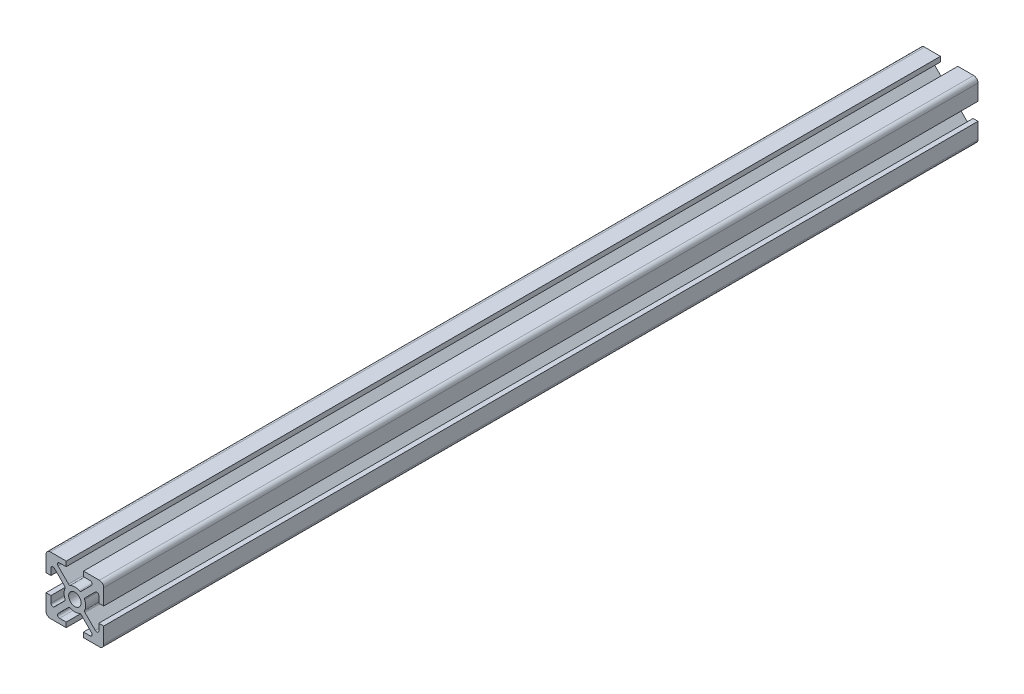
SolidWorks part; units mm, degrees
material "6063-T5"
ref_plane "Face" through (0, 0, 0) normal (0, 0, 1) x (1, 0, 0)
ref_plane "Dessus" through (0, 0, 0) normal (0, 1, 0) x (1, 0, 0)
ref_plane "Droite" through (0, 0, 0) normal (1, 0, 0) x (0, 0, -1)
sketch "Esquisse1" plane through (0, 0, 0) normal (0, 0, 1) x (1, 0, 0)
  line L0 (-3, 10) -> (-8.5, 10)
  line L2 (-3, -10) -> (-3, -8.3)
  line L3 (-3, -8.3) -> (-5.2994, -8.3)
  line L4 (-5.7944, -7.105) -> (-2.1755, -3.4861)
  line L6 (2.1755, -3.4861) -> (5.7944, -7.105)
  line L7 (5.2994, -8.3) -> (3, -8.3)
  line L8 (3, -8.3) -> (3, -10)
  line L11 (3, -10) -> (8.5, -10)
  line L12 (10, -8.5) -> (10, -3)
  line L15 (10, -3) -> (8.3, -3)
  line L16 (8.3, -3) -> (8.3, -5.2994)
  line L17 (7.105, -5.7944) -> (3.4861, -2.1755)
  line L20 (3.4861, 2.1755) -> (7.105, 5.7944)
  line L21 (8.3, 5.2994) -> (8.3, 3)
  line L22 (8.3, 3) -> (10, 3)
  line L25 (10, 3) -> (10, 8.5)
  line L26 (8.5, 10) -> (3.5, 10)
  line L29 (3, 10) -> (3, 8.3)
  line L30 (3, 8.3) -> (5.2994, 8.3)
  line L31 (5.7944, 7.105) -> (2.1755, 3.4861)
  line L34 (-2.1755, 3.4861) -> (-5.7944, 7.105)
  line L35 (-5.2994, 8.3) -> (-3, 8.3)
  line L36 (-3, 8.3) -> (-3, 10)
  line L39 (3.5, 10) -> (3, 10)
  line L40 (-10, 8.5) -> (-10, 3)
  line L43 (-10, 3) -> (-8.3, 3)
  line L44 (-8.3, 3) -> (-8.3, 5.2994)
  line L45 (-7.105, 5.7944) -> (-3.4861, 2.1755)
  line L48 (-3.4861, -2.1755) -> (-7.105, -5.7944)
  line L49 (-8.3, -5.2994) -> (-8.3, -3)
  line L50 (-8.3, -3) -> (-10, -3)
  line L53 (-10, -3) -> (-10, -8.5)
  line L54 (-8.5, -10) -> (-3, -10)
  line L55 (13.1941, 0) -> (-16.3684, 0) construction
  line L56 (0, 3.75) -> (0, -15.1011) construction
  line L58 (5.7944, 5.7944) -> (-5.2994, -5.2994) construction
  line L59 (5.7944, -5.7944) -> (-5.4107, 5.4107) construction
  circle A0 centre (0, 0) radius 2.15
  arc A1 (-5.2994, -8.3) -> (-5.7944, -7.105) centre (-5.2994, -7.6) cw
  arc A2 (-2.1755, -3.4861) -> (-1.6076, -3.388) centre (-1.8219, -3.8397) cw
  arc A3 (-1.6076, -3.388) -> (1.6076, -3.388) centre (0, 0) ccw
  arc A5 (1.6076, -3.388) -> (2.1755, -3.4861) centre (1.8219, -3.8397) cw
  arc A6 (5.7944, -7.105) -> (5.2994, -8.3) centre (5.2994, -7.6) cw
  arc A7 (8.5, -10) -> (10, -8.5) centre (8.5, -8.5) ccw
  arc A8 (8.3, -5.2994) -> (7.105, -5.7944) centre (7.6, -5.2994) cw
  arc A9 (3.4861, -2.1755) -> (3.388, -1.6076) centre (3.8397, -1.8219) cw
  arc A10 (3.388, -1.6076) -> (3.75, 0) centre (0, 0) ccw
  arc A11 (3.75, 0) -> (3.388, 1.6076) centre (0, 0) ccw
  arc A12 (3.388, 1.6076) -> (3.4861, 2.1755) centre (3.8397, 1.8219) cw
  arc A13 (7.105, 5.7944) -> (8.3, 5.2994) centre (7.6, 5.2994) cw
  arc A14 (10, 8.5) -> (8.5, 10) centre (8.5, 8.5) ccw
  arc A15 (5.2994, 8.3) -> (5.7944, 7.105) centre (5.2994, 7.6) cw
  arc A16 (2.1755, 3.4861) -> (1.6076, 3.388) centre (1.8219, 3.8397) cw
  arc A17 (1.6076, 3.388) -> (-1.6076, 3.388) centre (0, 0) ccw
  arc A19 (-1.6076, 3.388) -> (-2.1755, 3.4861) centre (-1.8219, 3.8397) cw
  arc A20 (-5.7944, 7.105) -> (-5.2994, 8.3) centre (-5.2994, 7.6) cw
  arc A21 (-8.5, 10) -> (-10, 8.5) centre (-8.5, 8.5) ccw
  arc A22 (-8.3, 5.2994) -> (-7.105, 5.7944) centre (-7.6, 5.2994) cw
  arc A23 (-3.4861, 2.1755) -> (-3.388, 1.6076) centre (-3.8397, 1.8219) cw
  arc A24 (-3.388, 1.6076) -> (-3.388, -1.6076) centre (0, 0) ccw
  arc A26 (-3.388, -1.6076) -> (-3.4861, -2.1755) centre (-3.8397, -1.8219) cw
  arc A27 (-7.105, -5.7944) -> (-8.3, -5.2994) centre (-7.6, -5.2994) cw
  arc A28 (-10, -8.5) -> (-8.5, -10) centre (-8.5, -8.5) ccw
  dimension "D3" = 4.3
  dimension "D4" = 1.5
  dimension "D15" = 0.7
  dimension "D19" = 3.75
  dimension "D20" = 0.5
  dimension "D1" = 20
  dimension "D2" = 20
  dimension "D10" = 10
  dimension "D11" = 10
  dimension "D12" = 3
  dimension "D13" = 3
  dimension "D16" = 1.7
  dimension "D17" = 5.2994
  dimension "D18" = 45
  dimension "D22" = 45
  dimension "D23" = 6
  dimension "D24" = 45
  dimension "D25" = 5.2994
  dimension "D26" = 45
extrude "Boss.-Extru.1" add sketch "Esquisse1" along normal blind 303
